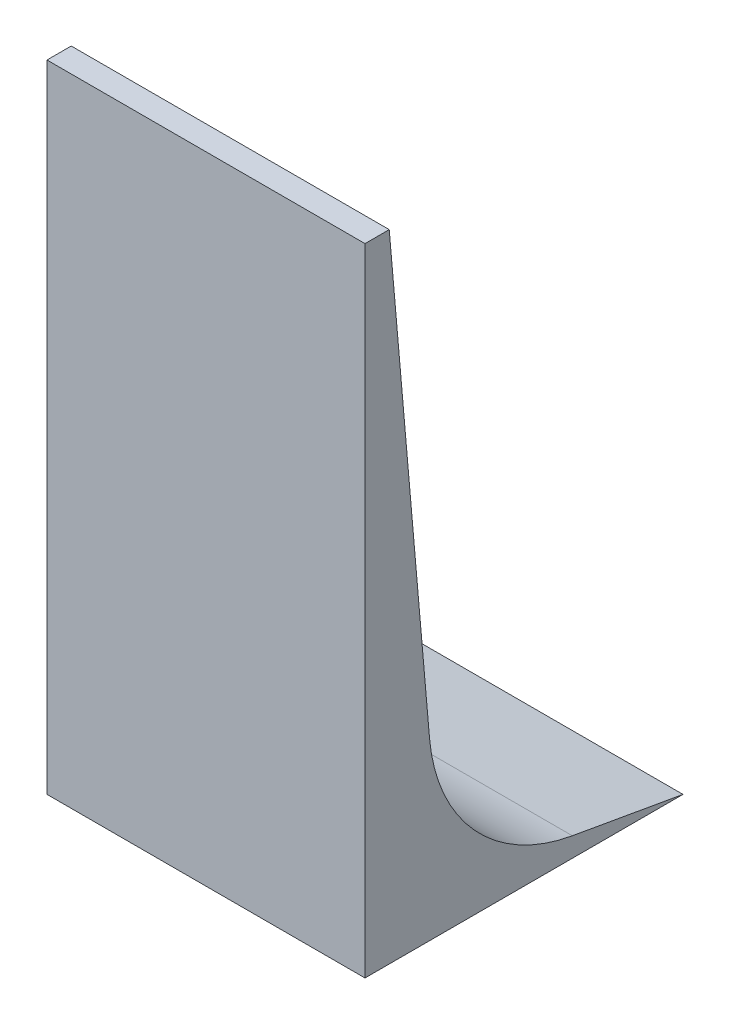
SolidWorks part; units mm, degrees
material "AISI 1020"
ref_plane "Front Plane" through (0, 0, 0) normal (0, 0, 1) x (1, 0, 0)
ref_plane "Top Plane" through (0, 0, 0) normal (0, 1, 0) x (1, 0, 0)
ref_plane "Right Plane" through (0, 0, 0) normal (1, 0, 0) x (0, 0, -1)
sketch "Sketch1" plane through (0, 0, 0) normal (1, 0, 0) x (0, 0, -1)
  line L0 (38.1, 1000) -> (101.4671, 275.7104)
  line L1 (0, 0) -> (500, 0)
  line L2 (0, 0) -> (0, 1000)
  line L3 (0, 1000) -> (38.1, 1000)
  line L5 (500, 0) -> (325.9944, 30.6819)
  arc A0 (101.4671, 275.7104) -> (325.9944, 30.6819) centre (373.3945, 299.501) ccw
  point P9 (0, 0)
  point P10 (0, 0)
  dimension "D5" = 10
  dimension "D1" = 500
  dimension "D2" = 1000
  dimension "D3" = 85
  dimension "D4" = 38.1
extrude "Boss-Extrude1" add sketch "Sketch1" against normal blind 500
